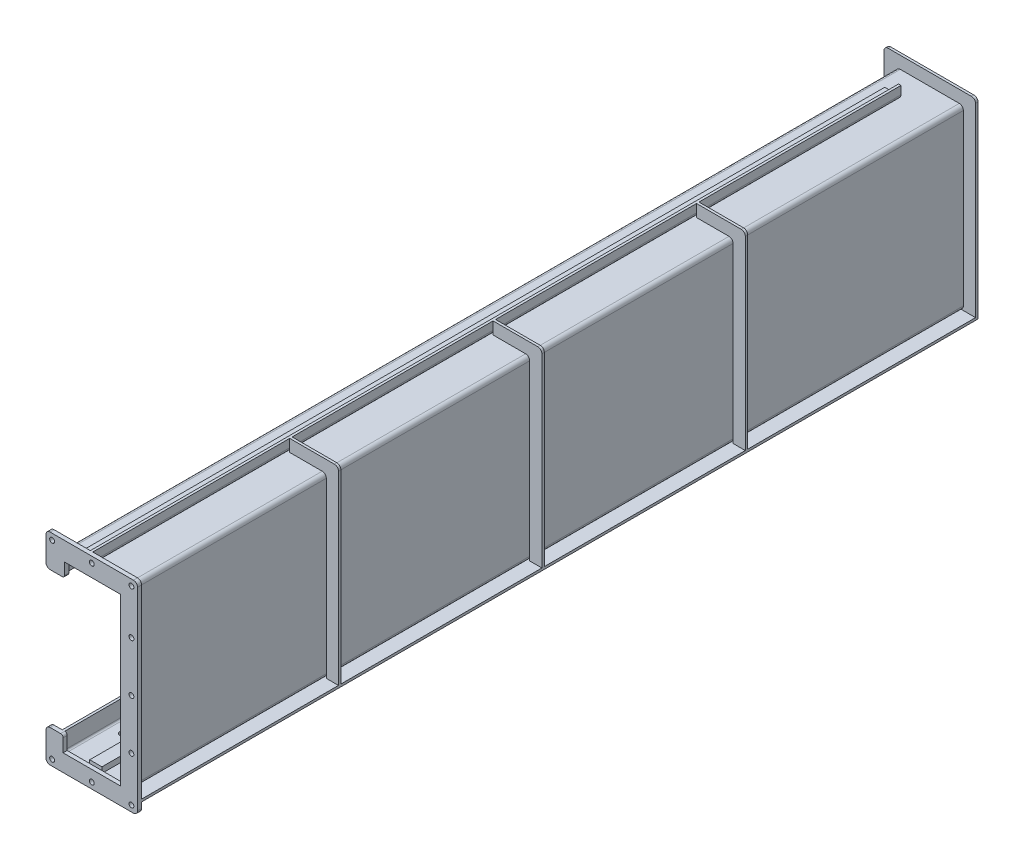
SolidWorks part; units mm, degrees
material "普通碳钢"
ref_plane "前视基准面" through (0, 0, 0) normal (0, 0, 1) x (1, 0, 0)
ref_plane "上视基准面" through (0, 0, 0) normal (0, 1, 0) x (1, 0, 0)
ref_plane "右视基准面" through (0, 0, 0) normal (1, 0, 0) x (0, 0, -1)
sketch "草图1" plane through (0, 0, 0) normal (0, 0, 1) x (1, 0, 0)
  line L2 (0, 10) -> (0, 426)
  line L13 (-165, 386) -> (-165, 426)
  line L15 (-159, 386) -> (-159, 426)
  line L16 (-159, 50) -> (-165, 50)
  line L17 (-159, 386) -> (-165, 386)
  line L18 (-6, 10) -> (-6, 426)
  line L19 (-10, 6) -> (-155, 6)
  line L20 (-159, 10) -> (-159, 50)
  line L21 (-165, 10) -> (-165, 50)
  line L22 (-10, 436) -> (-155, 436)
  line L23 (-10, 0) -> (-155, 0)
  line L24 (-10, 430) -> (-155, 430)
  arc A8 (-6, 426) -> (-10, 430) centre (-10, 426) ccw
  arc A9 (-10, 6) -> (-6, 10) centre (-10, 10) ccw
  arc A10 (-155, 6) -> (-159, 10) centre (-155, 10) cw
  arc A11 (-155, 430) -> (-159, 426) centre (-155, 426) ccw
  arc A12 (0, 426) -> (-10, 436) centre (-10, 426) ccw
  arc A13 (-155, 436) -> (-165, 426) centre (-155, 426) ccw
  arc A14 (-10, 0) -> (0, 10) centre (-10, 10) ccw
  arc A15 (-155, 0) -> (-165, 10) centre (-155, 10) cw
  point P0 (-82.5, 0)
  point P5 (165, 10)
  point P9 (0, 0)
  point P11 (165, 426)
  point P15 (0, 436)
  point P19 (159, 426)
  point P20 (159, 10)
  point P34 (-165, 436)
  dimension "D3" = 6
  dimension "D10" = 10
  dimension "D11" = 4
  dimension "D12" = 10
  dimension "D13" = 4
  dimension "D14" = 10
  dimension "D15" = 4
  dimension "D16" = 10
  dimension "D17" = 4
  dimension "D1" = 436
  dimension "D2" = 165
  dimension "D5" = 6
  dimension "D6" = 6
  dimension "D4" = 6
  dimension "D7" = 6
  dimension "D8" = 50
  dimension "D9" = 50
extrude "凸台-拉伸1" add sketch "草图1" along normal blind 2050
sketch "草图2" plane through (0, 0, 2050) normal (0, 0, 1) x (1, 0, 0)
  line L5 (-165, 50) -> (-165, 10) construction
  line L7 (-165, 426) -> (-165, 386) construction
  line L8 (-10, 436) -> (-155, 436) construction
  line L10 (0, 10) -> (0, 426) construction
  line L16 (-155, 0) -> (-10, 0) construction
  line L23 (-153, 50) -> (-195, 50)
  line L39 (-149, 386) -> (-149, 426)
  line L40 (-149, 386) -> (-149, 420)
  line L47 (-155, 420) -> (-10, 420)
  line L48 (-149, 420) -> (-12, 420)
  line L50 (-12, 426) -> (-12, 10)
  line L51 (-12, 420) -> (-12, 12)
  line L53 (-10, 12) -> (-155, 12)
  line L54 (-12, 12) -> (-153, 12)
  line L56 (-153, 10) -> (-153, 50)
  line L57 (-153, 12) -> (-153, 50)
  line L64 (-195, 50) -> (-195, -20)
  line L65 (-185, -30) -> (20, -30)
  line L66 (30, -20) -> (30, 456)
  line L67 (20, 466) -> (-185, 466)
  line L68 (-195, 456) -> (-195, 386)
  line L69 (-195, 386) -> (-149, 386)
  arc A0 (-195, 456) -> (-185, 466) centre (-185, 456) cw
  arc A13 (30, 456) -> (20, 466) centre (20, 456) ccw
  arc A14 (20, -30) -> (30, -20) centre (20, -20) ccw
  arc A15 (-185, -30) -> (-195, -20) centre (-185, -20) cw
  dimension "D5" = 6
  dimension "D10" = 30
  dimension "D6" = 10
  dimension "D1" = 10
  dimension "D2" = 10
  dimension "D3" = 6
  dimension "D4" = 6
  dimension "D7" = 30
  dimension "D8" = 30
  dimension "D9" = 30
  dimension "D11" = 30
extrude "凸台-拉伸2" add sketch "草图2" along normal blind 10 separate body
ref_plane "基准面1" through (0, 0, 1560) normal (0, 0, 1) x (1, 0, 0)
ref_plane "基准面2" through (0, 0, 1060) normal (0, 0, 1) x (1, 0, 0)
ref_plane "基准面3" through (0, 0, 560) normal (0, 0, 1) x (1, 0, 0)
sketch "草图3" plane through (0, 436, 0) normal (0, 1, 0) x (1, 0, 0)
  line L0 (-10, -2050) -> (-10, 0) construction
  line L1 (-90, -63.2921) -> (-130, -63.2921)
  line L2 (-90, -63.2921) -> (-90, -2050)
  line L4 (-130, -63.2921) -> (-130, -2050)
  line L7 (-90, -2050) -> (-130, -2050)
  dimension "D1" = 40
  dimension "D2" = 80
extrude "凸台-拉伸3" add sketch "草图3" along normal blind 6 separate body
sketch "草图4" plane through (0, 442, 0) normal (0, 1, 0) x (1, 0, 0)
  line L0 (-130, -2050) -> (-90, -2050) construction
  line L1 (-96, -63.2921) -> (-90, -63.2921)
  line L2 (-96, -63.2921) -> (-96, -2050)
  line L3 (-96, -2050) -> (-90, -2050)
  line L4 (-90, -63.2921) -> (-90, -2050)
  line L5 (-90, -2050) -> (-90, -63.2921) construction
  dimension "D1" = 6
extrude "凸台-拉伸4" add sketch "草图4" along normal blind 24
fillet "圆角1" radius 4 1 edges at (-96, 442, 1056.6461)
fillet "圆角2" radius 10 1 edges at (-90, 436, 1056.6461)
sketch "草图5" plane through (0, 0, 1560) normal (0, 0, 1) x (1, 0, 0)
  line L0 (0, 0) -> (30, 0)
  line L1 (0, 0) -> (0, 426)
  line L2 (-10, 436) -> (-90, 436)
  line L4 (-90, 466) -> (-90, 436)
  line L5 (-90, 466) -> (-90, 446) construction
  line L17 (-12, 420) -> (-12, 12)
  line L19 (-149, 420) -> (-12, 420)
  line L21 (-149, 386) -> (-149, 420)
  line L23 (-195, 386) -> (-149, 386)
  line L25 (-195, 456) -> (-195, 386)
  line L27 (20, 466) -> (-90, 466)
  line L28 (20, 466) -> (-90, 466)
  line L29 (30, -20) -> (30, 456)
  line L30 (30, 0) -> (30, 456)
  line L31 (-185, -30) -> (20, -30)
  line L33 (-195, 50) -> (-195, -20)
  line L35 (-153, 50) -> (-195, 50)
  line L37 (-153, 12) -> (-153, 50)
  line L39 (-12, 12) -> (-153, 12)
  line L65 (-130, 442) -> (-100, 442)
  line L66 (-90, 466) -> (-90, 446)
  line L67 (-96, 446) -> (-96, 466)
  line L68 (-100, 436) -> (-130, 436)
  line L70 (-96, 466) -> (-185, 466)
  line L75 (-130, 436) -> (-130, 442)
  arc A3 (0, 426) -> (-10, 436) centre (-10, 426) ccw construction
  arc A5 (0, 426) -> (-10, 436) centre (-10, 426) ccw
  arc A14 (-185, 466) -> (-195, 456) centre (-185, 456) ccw
  arc A24 (-100, 442) -> (-96, 446) centre (-100, 446) ccw
  arc A25 (-100, 436) -> (-90, 446) centre (-100, 446) ccw
  arc A29 (30, 456) -> (20, 466) centre (20, 456) ccw
  arc A30 (30, 456) -> (20, 466) centre (20, 456) ccw
  arc A31 (20, -30) -> (30, -20) centre (20, -20) ccw
  arc A33 (-195, -20) -> (-185, -30) centre (-185, -20) ccw
  dimension "D1" = 0
extrude "凸台-拉伸5" add sketch "草图5" along normal blind 6
sketch "草图6" plane through (0, 0, 1060) normal (0, 0, 1) x (1, 0, 0)
  line L6 (-90, 436) -> (-10, 436)
  line L7 (-90, 436) -> (-10, 436)
  line L8 (0, 10) -> (0, 0)
  line L10 (0, 10) -> (0, 0)
  line L11 (0, 0) -> (30, 0)
  line L12 (0, 0) -> (30, 0)
  line L13 (-90, 446) -> (-90, 436)
  line L21 (-90, 446) -> (-90, 436)
  line L25 (0, 426) -> (0, 10)
  line L26 (0, 426) -> (0, 10)
  line L27 (-90, 466) -> (-90, 446)
  line L28 (-90, 466) -> (-90, 446)
  line L29 (20, 466) -> (-90, 466)
  line L30 (20, 466) -> (-90, 466)
  line L31 (30, 0) -> (30, 456)
  line L32 (30, 0) -> (30, 456)
  arc A2 (30, 456) -> (20, 466) centre (20, 456) ccw
  arc A3 (30, 456) -> (20, 466) centre (20, 456) ccw
  arc A9 (0, 426) -> (-10, 436) centre (-10, 426) ccw
  arc A10 (0, 426) -> (-10, 436) centre (-10, 426) ccw
  dimension "D1" = 0
extrude "凸台-拉伸6" add sketch "草图6" along normal blind 6
sketch "草图7" plane through (0, 0, 560) normal (0, 0, 1) x (1, 0, 0)
  line L5 (0, 426) -> (0, 10)
  line L9 (0, 426) -> (0, 10)
  line L11 (0, 10) -> (0, 0)
  line L12 (0, 10) -> (0, 0)
  line L14 (-90, 446) -> (-90, 436)
  line L22 (-90, 446) -> (-90, 436)
  line L29 (0, 0) -> (30, 0)
  line L30 (0, 0) -> (30, 0)
  line L31 (-90, 436) -> (-10, 436)
  line L32 (-90, 436) -> (-10, 436)
  line L33 (-90, 466) -> (-90, 446)
  line L34 (-90, 466) -> (-90, 446)
  line L35 (20, 466) -> (-90, 466)
  line L36 (20, 466) -> (-90, 466)
  line L37 (30, 0) -> (30, 456)
  line L38 (30, 0) -> (30, 456)
  arc A2 (0, 426) -> (-10, 436) centre (-10, 426) ccw
  arc A3 (0, 426) -> (-10, 436) centre (-10, 426) ccw
  arc A5 (30, 456) -> (20, 466) centre (20, 456) ccw
  arc A11 (30, 456) -> (20, 466) centre (20, 456) ccw
  dimension "D1" = 0
extrude "凸台-拉伸7" add sketch "草图7" along normal blind 6
sketch "草图8" plane through (0, 0, 0) normal (0, 0, -1) x (-1, 0, 0)
  line L3 (0, 0) -> (-30, 0)
  line L4 (0, 0) -> (195, 0)
  line L14 (153, 12) -> (12, 12)
  line L16 (153, 12) -> (12, 12)
  line L17 (153, 50) -> (153, 12)
  line L18 (153, 50) -> (153, 12)
  line L19 (195, 50) -> (153, 50)
  line L20 (195, 50) -> (153, 50)
  line L21 (195, -20) -> (195, 50)
  line L22 (195, 0) -> (195, 50)
  line L23 (-20, -30) -> (185, -30)
  line L25 (-30, 456) -> (-30, -20)
  line L26 (-30, 456) -> (-30, 0)
  line L27 (185, 466) -> (-20, 466)
  line L29 (185, 466) -> (-20, 466)
  line L31 (195, 386) -> (195, 456)
  line L38 (195, 386) -> (195, 456)
  line L39 (149, 386) -> (195, 386)
  line L40 (149, 386) -> (195, 386)
  line L41 (149, 420) -> (149, 386)
  line L42 (149, 420) -> (149, 386)
  line L43 (12, 420) -> (149, 420)
  line L44 (12, 420) -> (149, 420)
  line L45 (12, 12) -> (12, 420)
  line L46 (12, 12) -> (12, 420)
  arc A10 (185, -30) -> (195, -20) centre (185, -20) ccw
  arc A20 (-30, -20) -> (-20, -30) centre (-20, -20) ccw
  arc A23 (-20, 466) -> (-30, 456) centre (-20, 456) ccw
  arc A24 (-20, 466) -> (-30, 456) centre (-20, 456) ccw
  arc A25 (195, 456) -> (185, 466) centre (185, 456) ccw
  arc A26 (195, 456) -> (185, 466) centre (185, 456) ccw
  dimension "D1" = 0
extrude "凸台-拉伸8" add sketch "草图8" along normal blind 6
sketch "草图9" plane through (0, 0, 0) normal (0, -1, 0) x (1, 0, 0)
  line L1 (-150, -6) -> (30, -6)
  line L2 (-150, -6) -> (-150, 2050)
  line L3 (-150, 2050) -> (30, 2050)
  line L4 (30, -6) -> (30, 2050)
  line L5 (30, -6) -> (-195, -6) construction
  dimension "D1" = 180
extrude "凸台-拉伸9" add sketch "草图9" along normal blind 6
sketch "草图10" plane through (0, 0, 2050) normal (0, 0, 1) x (1, 0, 0)
  line L0 (-67.5, 430) -> (-97.5, 430)
  line L1 (-97.5, 6) -> (-67.5, 6)
  line L2 (-97.5, 6) -> (-97.5, 20)
  line L3 (-97.5, 20) -> (-67.5, 20)
  line L4 (-67.5, 6) -> (-67.5, 20)
  line L5 (-10, 6) -> (-155, 6) construction
  line L6 (-155, 430) -> (-10, 430) construction
  line L8 (-97.5, 430) -> (-97.5, 416)
  line L9 (-97.5, 416) -> (-67.5, 416)
  line L10 (-67.5, 430) -> (-67.5, 416)
  line L14 (-6, 426) -> (-6, 10) construction
  dimension "D1" = 30
  dimension "D2" = 14
  dimension "D3" = 61.5
  dimension "D4" = 14
  dimension "D5" = 30
extrude "凸台-拉伸10" add sketch "草图10" against normal up to surface (2056 mm away)
fillet "圆角3" radius 10 2 edges at (-195, 386, 2055) (-195, 50, 2055)
fillet "圆角4" radius 6 2 edges at (-153, 50, 2055) (-149, 386, 2055)
sketch "草图11" plane through (0, 6, 0) normal (0, 1, 0) x (1, 0, 0)
  line L0 (-127.5, -2050) -> (-127.5, 0) construction
  line L1 (-97.5, -2050) -> (-155, -2050) construction
  line L2 (-37.5, -2050) -> (-37.5, 0) construction
  line L3 (-10, -2050) -> (-67.5, -2050) construction
  line L4 (-10, -1940) -> (-150.7283, -1940) construction
  line L5 (-10, -2050) -> (-10, 0) construction
  line L7 (-67.5, 0) -> (-67.5, -2050) construction
  line L8 (-97.5, 0) -> (-97.5, -2050) construction
  line L10 (-10, -1700) -> (-150.7283, -1700) construction
  line L11 (-10, -1460) -> (-150.7283, -1460) construction
  line L12 (-10, -1220) -> (-150.7283, -1220) construction
  line L13 (-10, -980) -> (-150.7283, -980) construction
  line L14 (-10, -740) -> (-150.7283, -740) construction
  line L15 (-10, -500) -> (-150.7283, -500) construction
  line L16 (-10, -260) -> (-150.7283, -260) construction
  line L17 (-10, -20) -> (-150.7283, -20) construction
  line L19 (-10, 0) -> (-67.5, 0) construction
  circle A0 centre (-37.5, -1940) radius 7
  circle A1 centre (-127.5, -1940) radius 7
  circle A2 centre (-37.5, -1700) radius 7
  circle A3 centre (-127.5, -1700) radius 7
  circle A4 centre (-37.5, -1460) radius 7
  circle A5 centre (-127.5, -1460) radius 7
  circle A6 centre (-37.5, -1220) radius 7
  circle A7 centre (-127.5, -1220) radius 7
  circle A8 centre (-37.5, -980) radius 7
  circle A9 centre (-127.5, -980) radius 7
  circle A10 centre (-37.5, -740) radius 7
  circle A11 centre (-127.5, -740) radius 7
  circle A12 centre (-37.5, -500) radius 7
  circle A13 centre (-127.5, -500) radius 7
  circle A14 centre (-37.5, -260) radius 7
  circle A15 centre (-127.5, -260) radius 7
  circle A16 centre (-37.5, -20) radius 7
  circle A17 centre (-127.5, -20) radius 7
  dimension "D4" = 14
  dimension "D1" = 30
  dimension "D2" = 30
  dimension "D3" = 20
  dimension "D6" = 240
  dimension "D5" = 9
extrude "切除-拉伸1" cut sketch "草图11" against normal up to next
sketch "草图12" plane through (0, 0, 2060) normal (0, 0, 1) x (1, 0, 0)
  line L0 (-195, 451) -> (30, 451) construction
  line L1 (-195, 456) -> (-195, 396) construction
  line L2 (30, -20) -> (30, 456) construction
  line L3 (-180, 466) -> (-180, -30) construction
  line L4 (20, 466) -> (-185, 466) construction
  line L5 (-185, -30) -> (20, -30) construction
  line L6 (-195, -15) -> (30, -15) construction
  line L7 (-195, 40) -> (-195, -20) construction
  line L8 (15, -30) -> (15, 466) construction
  line L9 (-195, 95) -> (30, 95) construction
  line L22 (-5755.0612, -422) -> (-60.0612, -422)
  line L23 (-60.0612, -422) -> (-60.0612, -88)
  line L24 (-60.0612, -88) -> (-5755.0612, -88)
  line L25 (-5755.0612, -88) -> (-5755.0612, -422)
  line L30 (-195, 341) -> (30, 341) construction
  circle A0 centre (-180, 451) radius 6
  circle A1 centre (-82.5, 451) radius 6
  circle A2 centre (15, 451) radius 6
  circle A3 centre (15, 341) radius 6
  circle A4 centre (15, 95) radius 6
  circle A5 centre (15, 218) radius 6
  circle A6 centre (15, -15) radius 6
  circle A7 centre (-82.5, -15) radius 6
  circle A8 centre (-180, -15) radius 6
  dimension "D7" = 12
  dimension "D1" = 15
  dimension "D2" = 15
  dimension "D3" = 15
  dimension "D4" = 15
  dimension "D5" = 110
  dimension "D6" = 110
extrude "切除-拉伸2" cut sketch "草图12" against normal blind 10
